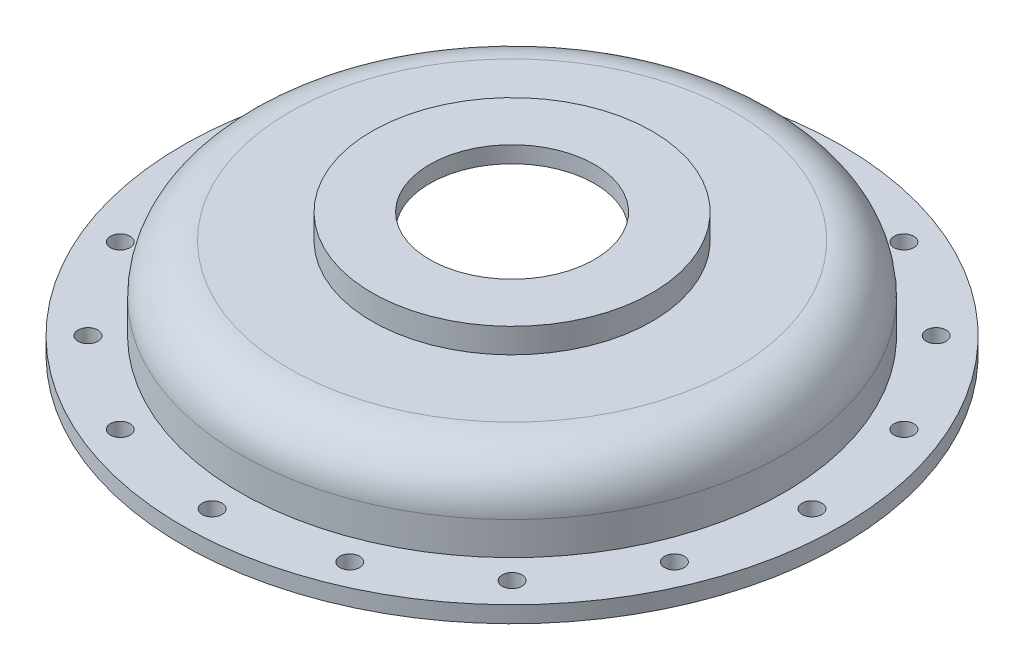
SolidWorks part; units mm, degrees
ref_plane "Front Plane" through (0, 0, 0) normal (0, 0, 1) x (1, 0, 0)
ref_plane "Top Plane" through (0, 0, 0) normal (0, 1, 0) x (1, 0, 0)
ref_plane "Right Plane" through (0, 0, 0) normal (1, 0, 0) x (0, 0, -1)
sketch "Sketch1" plane through (0, 0, 0) normal (0, 0, 1) x (1, 0, 0)
  line L0 (50, 0) -> (200, 0) construction
  line L1 (200, 0) -> (200, 10)
  line L2 (200, 10) -> (165, 10)
  line L5 (50, 0) -> (0, 0) construction
  line L6 (50, 0) -> (50, 75) construction
  line L7 (50, 75) -> (85, 75)
  line L8 (85, 75) -> (85, 60)
  line L9 (200, 0) -> (155, 0)
  line L12 (75, 50) -> (75, 65)
  line L13 (75, 65) -> (50, 65)
  line L14 (50, 65) -> (50, 75)
  line L15 (0, 0) -> (0, 125.085) construction
  line L16 (85, 60) -> (135, 60)
  line L17 (165, 30) -> (165, 10)
  line L18 (75, 50) -> (135, 50)
  line L19 (155, 30) -> (155, 0)
  arc A0 (135, 60) -> (165, 30) centre (135, 30) cw
  arc A1 (135, 50) -> (155, 30) centre (135, 30) cw
  point P2 (135.1266, 50)
  point P9 (0, 0)
  point P14 (182.5, 10)
  point P22 (0, 0)
  point P23 (0, 0)
  point P24 (155, 25.3244)
  point P25 (0, 0)
  point P26 (0, 0)
  point P27 (155, 14.8808)
  point P28 (0, 0)
  point P29 (165, 27.2589)
  dimension "D12" = 30
  dimension "D7" = 10
  dimension "D1" = 200
  dimension "D2" = 10
  dimension "D3" = 50
  dimension "D4" = 85
  dimension "D5" = 10
  dimension "D6" = 75
  dimension "D8" = 165
  dimension "D9" = 15
  dimension "D10" = 10
  dimension "D11" = 10
revolve "Revolve1" add sketch "Sketch1" angle 360 about L15
sketch "Sketch2" plane through (0, 10, 0) normal (0, 1, 0) x (1, 0, 0)
  circle A0 centre (182, 0) radius 6
  circle A1 centre (0, 0) radius 182 construction
  point P5 (0, 0)
  point P6 (0, 0)
  point P7 (0, 0)
  dimension "D1" = 182
  dimension "D2" = 12
extrude "Cut-Extrude1" cut sketch "Sketch2" against normal through all
pattern_circular "CirPattern1" count 16 over 360 about axis through (0, 0, 0) along (0, 1, 0) of "Cut-Extrude1"
